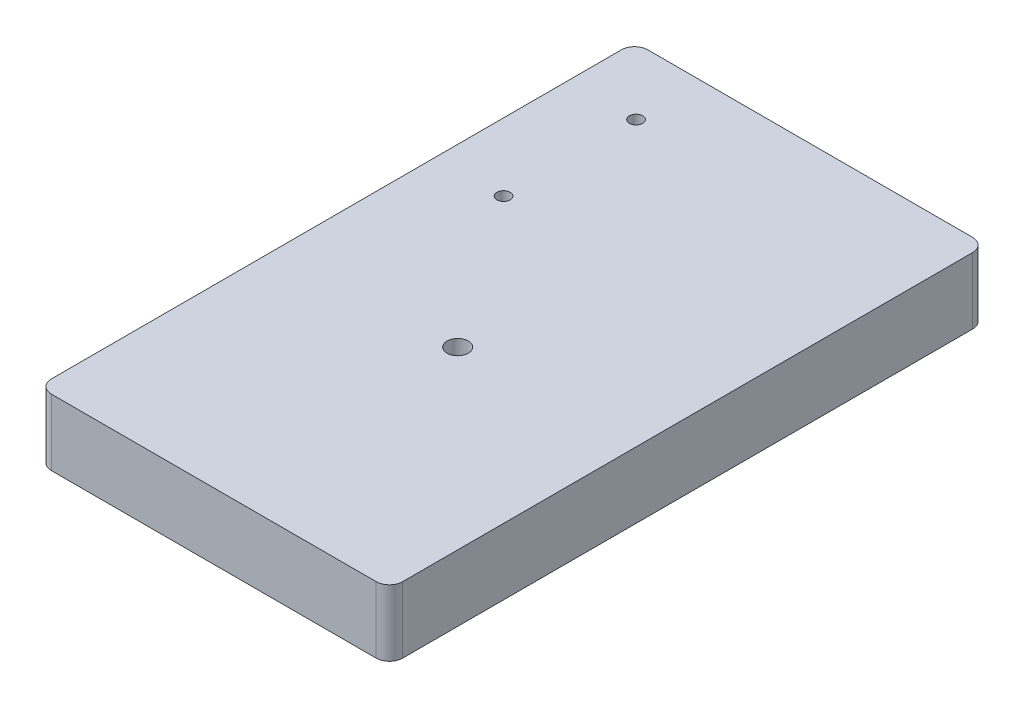
SolidWorks part; units mm, degrees
ref_plane "Plan de face" through (0, 0, 0) normal (0, 0, 1) x (1, 0, 0)
ref_plane "Plan de dessus" through (0, 0, 0) normal (0, 1, 0) x (1, 0, 0)
ref_plane "Plan de droite" through (0, 0, 0) normal (1, 0, 0) x (0, 0, -1)
sketch "Esquisse1" plane through (0, 0, 0) normal (0, 1, 0) x (1, 0, 0)
  line L6 (0, 88) -> (0, 2)
  line L7 (2, 0) -> (51, 0)
  line L8 (53, 88) -> (53, 2)
  line L11 (2, 90) -> (51, 90)
  arc A0 (51, 90) -> (53, 88) centre (51, 88) cw
  arc A1 (2, 90) -> (0, 88) centre (2, 88) ccw
  arc A2 (51, 0) -> (53, 2) centre (51, 2) ccw
  arc A3 (0, 2) -> (2, 0) centre (2, 2) ccw
  circle A4 centre (26.5, 36.8) radius 1.6
  point P2 (26.5, 0)
  point P3 (26.5, 0)
  dimension "D3" = 2
  dimension "D7" = 53.2
  dimension "D5" = 2
  dimension "D4" = 2
  dimension "D6" = 3.2
  dimension "D1" = 53
  dimension "D2" = 90
extrude "Extrusion1" add sketch "Esquisse1" along normal blind 10
sketch "Esquisse2" plane through (0, 0, 0) normal (0, -1, 0) x (1, 0, 0)
  line L0 (57.4636, -79) -> (-27.3834, -79) construction
  line L1 (-17.6242, -59.5) -> (57.4636, -59.5) construction
  line L2 (57.4636, -40) -> (-27.3834, -40) construction
  line L3 (57.4636, -20) -> (-27.3834, -20) construction
  line L4 (53, -103.2829) -> (53, 4.7947) construction
  line L5 (57.4636, -10) -> (-27.3834, -10) construction
  line L6 (48, -121.675) -> (48, 4.7947) construction
  line L7 (42, -111.2442) -> (42, 4.7947) construction
  line L8 (57.4636, -90) -> (-27.3834, -90) construction
  line L9 (57.4636, -85) -> (-27.3834, -85) construction
  line L10 (33, -121.675) -> (33, -69.6956) construction
  line L11 (41, -103.2829) -> (41, -69.6956) construction
  line L12 (57.4636, -49.5) -> (28.6431, -49.5) construction
  line L13 (37.3159, -82) -> (19.2671, -82) construction
  line L14 (45, -57.6837) -> (45, -3.061) construction
  line L15 (42, -49.5) -> (49.9748, -57.4748) construction
  line L16 (41, -82.7373) -> (41, -81.2627)
  line L17 (41, -85) -> (33.7489, -77.7489) construction
  line L18 (45.7373, -49.5) -> (44.2627, -49.5)
  line L19 (45.7373, -69.5) -> (44.2627, -69.5)
  line L20 (25, -82.7373) -> (25, -81.2627)
  line L21 (38.7373, -85) -> (27.2627, -85)
  line L22 (38.7373, -79) -> (27.2627, -79)
  line L23 (48, -67.2373) -> (48, -51.7627)
  line L24 (42, -67.2373) -> (42, -51.7627)
  line L25 (24, -67.2373) -> (24, -51.7627)
  line L26 (18, -67.2373) -> (18, -51.7627)
  line L27 (20.2627, -69.5) -> (21.7373, -69.5)
  line L28 (20.2627, -49.5) -> (21.7373, -49.5)
  line L29 (57.4636, -7) -> (6.2084, -7) construction
  line L30 (57.4636, -23) -> (6.2084, -23) construction
  arc A0 (44.2627, -49.5) -> (42, -51.7627) centre (43.1314, -50.6314) ccw
  arc A1 (38.7373, -85) -> (41, -82.7373) centre (39.8686, -83.8686) ccw
  arc A2 (38.7373, -79) -> (41, -81.2627) centre (39.8686, -80.1314) cw
  arc A3 (27.2627, -85) -> (25, -82.7373) centre (26.1314, -83.8686) cw
  arc A4 (27.2627, -79) -> (25, -81.2627) centre (26.1314, -80.1314) ccw
  arc A5 (45.7373, -49.5) -> (48, -51.7627) centre (46.8686, -50.6314) cw
  arc A6 (44.2627, -69.5) -> (42, -67.2373) centre (43.1314, -68.3686) cw
  arc A7 (45.7373, -69.5) -> (48, -67.2373) centre (46.8686, -68.3686) ccw
  arc A8 (20.2627, -69.5) -> (18, -67.2373) centre (19.1314, -68.3686) cw
  arc A9 (21.7373, -69.5) -> (24, -67.2373) centre (22.8686, -68.3686) ccw
  arc A10 (20.2627, -49.5) -> (18, -51.7627) centre (19.1314, -50.6314) ccw
  arc A11 (21.7373, -49.5) -> (24, -51.7627) centre (22.8686, -50.6314) cw
  circle A12 centre (45, -23) radius 1.1
  circle A13 centre (45, -7) radius 1.1
  dimension "D15" = 3
  dimension "D1" = 19.5
  dimension "D2" = 20
  dimension "D3" = 10
  dimension "D4" = 6
  dimension "D5" = 5
  dimension "D6" = 5
  dimension "D7" = 6
  dimension "D8" = 15
  dimension "D9" = 8
  dimension "D10" = 10
  dimension "D11" = 3
  dimension "D12" = 3
  dimension "D13" = 45
  dimension "D14" = 45
  dimension "D16" = 3
extrude "Enlèv. mat.-Extru.1" cut sketch "Esquisse2" against normal blind 4
sketch "Esquisse4" plane through (0, 10, 0) normal (0, 1, 0) x (1, 0, 0)
  line L0 (51, 90) -> (2, 90) construction
  circle A0 centre (10.2233, 80) radius 1
  circle A1 centre (10.2233, 60) radius 1
  dimension "D1" = 2
  dimension "D2" = 10
  dimension "D3" = 20
extrude "Enlèv. mat.-Extru.2" cut sketch "Esquisse4" against normal through all
